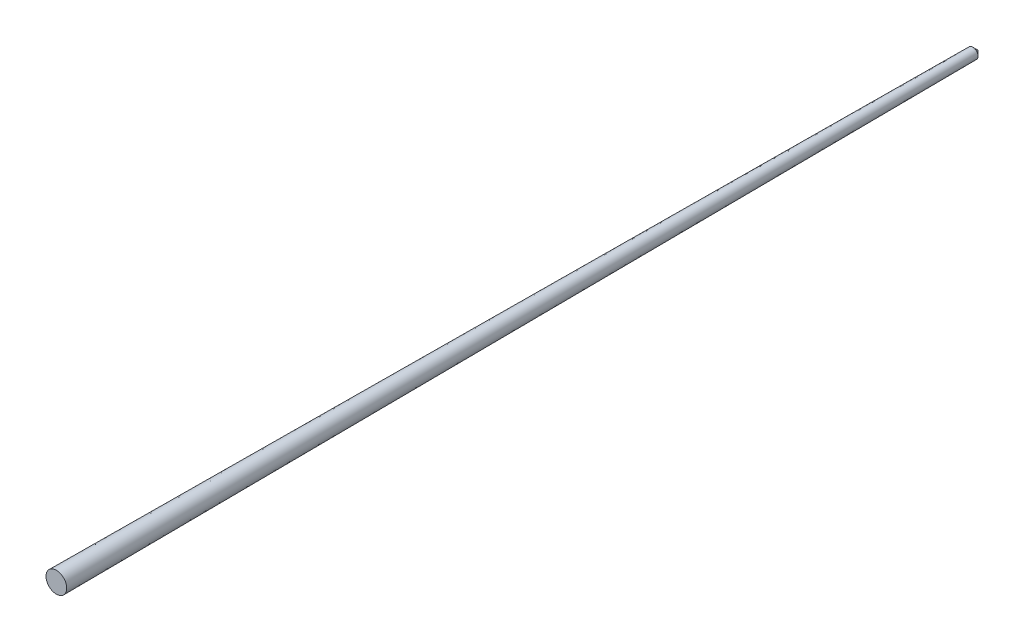
SolidWorks part; units mm, degrees
ref_plane "Front Plane" through (0, 0, 0) normal (0, 0, 1) x (1, 0, 0)
ref_plane "Top Plane" through (0, 0, 0) normal (0, 1, 0) x (1, 0, 0)
ref_plane "Right Plane" through (0, 0, 0) normal (1, 0, 0) x (0, 0, -1)
sketch "Sketch1" plane through (0, 0, 0) normal (0, 1, 0) x (1, 0, 0)
  line L0 (0, 0) -> (4.02, 0)
  line L1 (4.02, 0) -> (2.02, 355.6)
  line L3 (0, 355.6) -> (0, 0)
  line L4 (2.02, 355.6) -> (0, 357.62)
  line L5 (0, 357.62) -> (0, 355.6)
  point P5 (0, 0)
  point P7 (0, 0)
  point P8 (0, 0)
  dimension "D1" = 355.6
  dimension "D2" = 4.02
  dimension "D3" = 2.02
  dimension "D4" = 45
revolve "Revolve1" add sketch "Sketch1" angle 360 about L3
